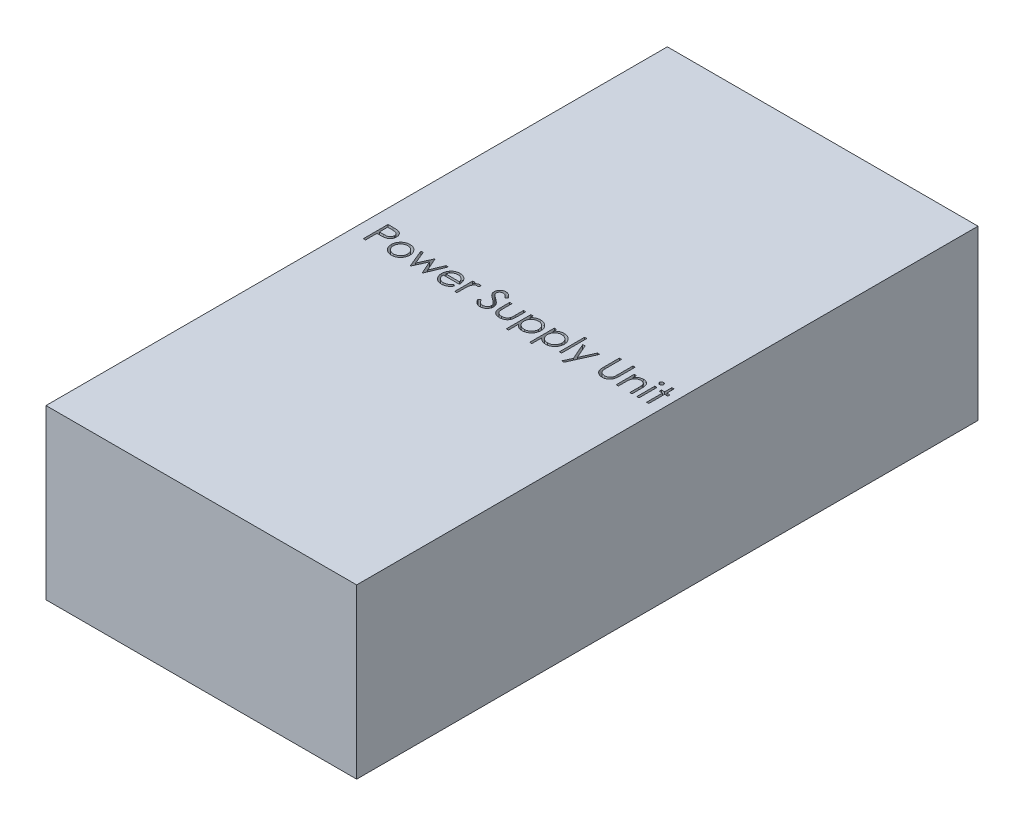
SolidWorks part; units mm, degrees
ref_plane "Front Plane" through (0, 0, 0) normal (0, 0, 1) x (1, 0, 0)
ref_plane "Top Plane" through (0, 0, 0) normal (0, 1, 0) x (1, 0, 0)
ref_plane "Right Plane" through (0, 0, 0) normal (1, 0, 0) x (0, 0, -1)
sketch "Sketch1" plane through (0, 0, 0) normal (0, 1, 0) x (1, 0, 0)
  line L1 (-60, -120) -> (60, -120)
  line L2 (-60, -120) -> (-60, 120)
  line L3 (-60, 120) -> (60, 120)
  line L4 (60, -120) -> (60, 120)
  line L5 (-60, -120) -> (60, 120) construction
  line L6 (-60, 120) -> (60, -120) construction
  point P0 (0, 0)
  dimension "D1" = 240
  dimension "D2" = 120
extrude "Boss-Extrude1" add sketch "Sketch1" along normal blind 65
sketch "Sketch2" plane through (0, 65, 0) normal (0, 1, 0) x (1, 0, 0)
  text T0 "Power Supply Unit" font "Century Gothic" height in points 36
  point P1 (0, 0)
extrude "Cut-Extrude1" cut sketch "Sketch2" against normal blind 12.93
